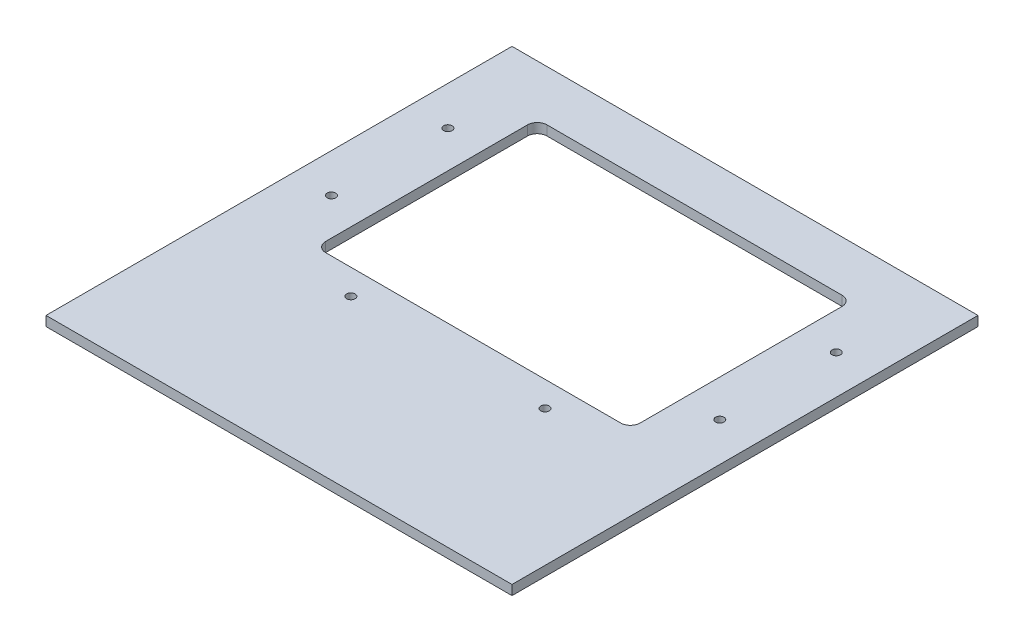
SolidWorks part; units mm, degrees
material "PBT General Purpose"
ref_plane "Front Plane" through (0, 0, 0) normal (0, 0, 1) x (1, 0, 0)
ref_plane "Top Plane" through (0, 0, 0) normal (0, 1, 0) x (1, 0, 0)
ref_plane "Right Plane" through (0, 0, 0) normal (1, 0, 0) x (0, 0, -1)
sketch "Sketch1" plane through (0, 0, 0) normal (0, 1, 0) x (1, 0, 0)
  line L0 (0, 44.6379) -> (0, -138.6591) construction
  line L1 (-152.4, 152.4) -> (152.4, 152.4)
  line L2 (-152.4, 152.4) -> (-152.4, -152.4)
  line L3 (-152.4, -152.4) -> (152.4, -152.4)
  line L4 (152.4, 152.4) -> (152.4, -152.4)
  line L5 (-152.4, 152.4) -> (152.4, -152.4) construction
  line L6 (-152.4, -152.4) -> (152.4, 152.4) construction
  line L7 (-96.5112, 119.38) -> (96.5112, 119.38)
  line L8 (-102.8612, 113.03) -> (-102.8612, -19.05)
  line L9 (-96.5112, -25.4) -> (96.5112, -25.4)
  line L10 (102.8612, 113.03) -> (102.8612, -19.05)
  line L11 (-34.8675, 0) -> (59.3168, 0) construction
  line L12 (-102.8612, 46.99) -> (102.8612, 46.99) construction
  line L13 (-101.0014, 117.5201) -> (101.0014, -23.5401) construction
  arc A0 (-102.8612, -19.05) -> (-96.5112, -25.4) centre (-96.5112, -19.05) ccw
  arc A1 (96.5112, -25.4) -> (102.8612, -19.05) centre (96.5112, -19.05) ccw
  arc A2 (96.5112, 119.38) -> (102.8612, 113.03) centre (96.5112, 113.03) cw
  arc A3 (-96.5112, 119.38) -> (-102.8612, 113.03) centre (-96.5112, 113.03) ccw
  circle A4 centre (-63.5, -41.91) radius 2.7781
  circle A5 centre (0, -41.91) radius 2.7781 construction
  circle A6 centre (63.5, -41.91) radius 2.7781
  circle A7 centre (127, 8.89) radius 2.7781
  circle A8 centre (127, 85.09) radius 2.7781
  circle A9 centre (-127, 8.89) radius 2.7781
  circle A10 centre (-127, 85.09) radius 2.7781
  point P0 (0, 0)
  point P18 (0, 119.38)
  point P41 (0, 0)
  dimension "D3" = 6.35
  dimension "D7" = 5.5562
  dimension "D1" = 304.8
  dimension "D2" = 304.8
  dimension "D4" = 246.38
  dimension "D5" = 144.78
  dimension "D6" = 127
  dimension "D8" = 127
  dimension "D9" = 76.2
  dimension "D10" = 88.9
  dimension "D11" = 127
  dimension "D12" = 193.0225
extrude "Boss-Extrude1" add sketch "Sketch1" along normal mid plane 6.35
